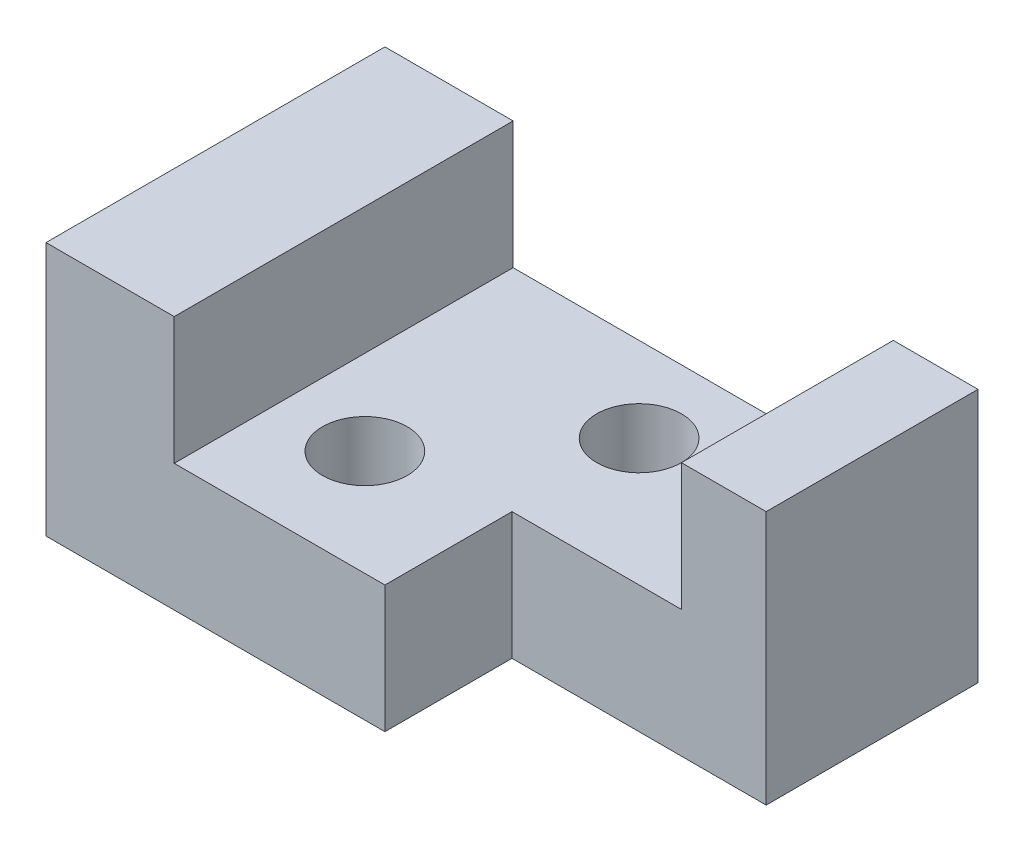
SolidWorks part; units mm, degrees
ref_plane "Front Plane" through (0, 0, 0) normal (0, 0, 1) x (1, 0, 0)
ref_plane "Top Plane" through (0, 0, 0) normal (0, 1, 0) x (1, 0, 0)
ref_plane "Right Plane" through (0, 0, 0) normal (1, 0, 0) x (0, 0, -1)
sketch "Sketch1" plane through (0, 0, 0) normal (0, 1, 0) x (1, 0, 0)
  line L1 (0, 0) -> (70, 0)
  line L2 (0, 0) -> (0, 40)
  line L3 (0, 40) -> (70, 40)
  line L4 (70, 0) -> (70, 40)
  dimension "D1" = 40
  dimension "D2" = 70
extrude "Boss-Extrude1" add sketch "Sketch1" along normal blind 30
sketch "Sketch2" plane through (0, 30, 0) normal (0, 1, 0) x (1, 0, 0)
  line L1 (40, 15) -> (70, 15)
  line L2 (40, 15) -> (40, 0)
  line L3 (40, 0) -> (70, 0)
  line L4 (70, 15) -> (70, 0)
  dimension "D1" = 15
  dimension "D2" = 30
extrude "Cut-Extrude1" cut sketch "Sketch2" against normal through all
sketch "Sketch3" plane through (0, 0, -40) normal (0, 0, -1) x (-1, 0, 0)
  line L0 (-70, 30) -> (0, 30) construction
  line L1 (-56.8626, 30) -> (-11.8626, 30)
  line L2 (-56.8626, 30) -> (-56.8626, 15)
  line L3 (-56.8626, 15) -> (-11.8626, 15)
  line L4 (-11.8626, 30) -> (-11.8626, 15)
  dimension "D1" = 15
  dimension "D2" = 45
extrude "Cut-Extrude2" cut sketch "Sketch3" against normal through all
sketch "Sketch4" plane through (0, 30, 0) normal (0, 1, 0) x (1, 0, 0)
  line L2 (0, 0) -> (15.1339, 0)
  line L3 (0, 0) -> (0, 40)
  line L4 (0, 40) -> (15.1339, 40)
  line L5 (15.1339, 0) -> (15.1339, 40)
  dimension "D1" = 15.1339
extrude "Boss-Extrude2" add sketch "Sketch4" against normal blind 15
sketch "Sketch6" plane through (0, 15, 0) normal (0, 1, 0) x (1, 0, 0)
  line L0 (40, 15) -> (40, 30) construction
  circle A0 centre (40, 30) radius 5
  dimension "D2" = 10
  dimension "D1" = 15
extrude "Cut-Extrude3" cut sketch "Sketch6" against normal through all contours A0
sketch "Sketch7" plane through (0, 15, 0) normal (0, 1, 0) x (1, 0, 0)
  line L0 (15.1339, 0) -> (25.1339, 0) construction
  line L1 (40, 0) -> (15.1339, 0) construction
  line L2 (25.1339, 0) -> (25.1339, 12.5) construction
  circle A0 centre (25.1339, 12.5) radius 5
  dimension "D3" = 10
  dimension "D1" = 10
  dimension "D2" = 12.5
extrude "Cut-Extrude4" cut sketch "Sketch7" against normal through all contours A0
sketch "Sketch8" plane through (0, 30, 0) normal (0, 1, 0) x (1, 0, 0)
  line L0 (70, 40) -> (60, 40) construction
  line L1 (70, 40) -> (56.8626, 40) construction
  line L3 (60, 40) -> (56.8626, 40)
  line L4 (60, 40) -> (60, 15)
  line L5 (60, 15) -> (56.8626, 15)
  line L6 (56.8626, 40) -> (56.8626, 15)
  dimension "D1" = 10
extrude "Cut-Extrude5" cut sketch "Sketch8" against normal blind 15
